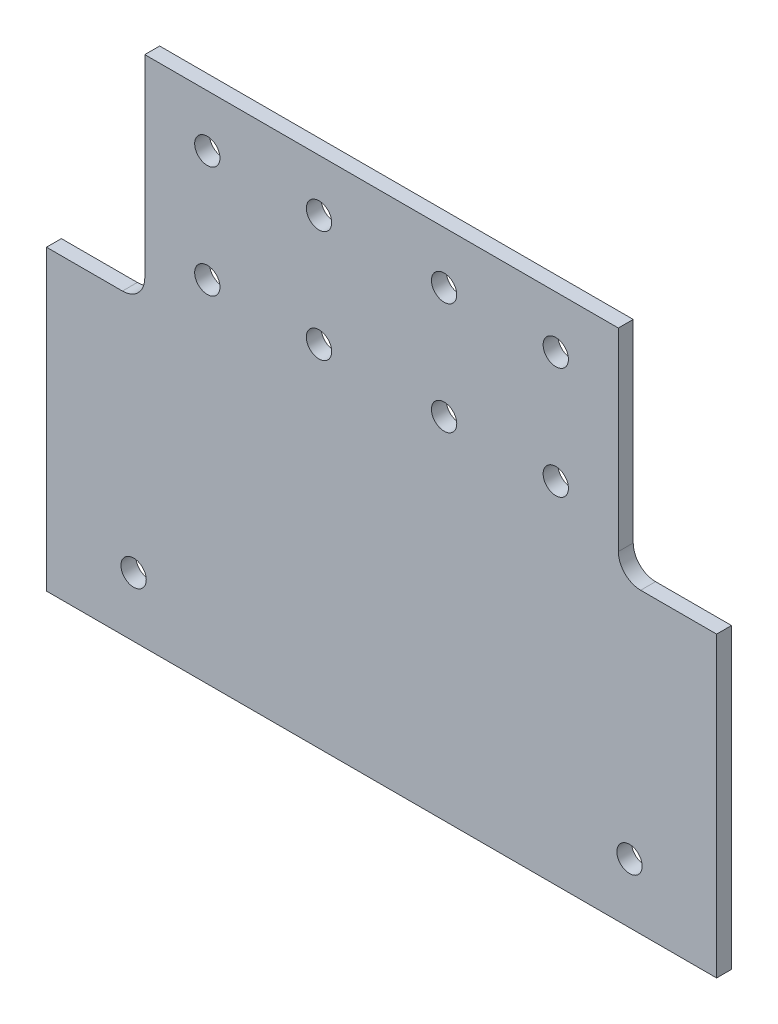
SolidWorks part; units mm, degrees
material "6061 Alloy"
ref_plane "Front Plane" through (0, 0, 0) normal (0, 0, 1) x (1, 0, 0)
ref_plane "Top Plane" through (0, 0, 0) normal (0, 1, 0) x (1, 0, 0)
ref_plane "Right Plane" through (0, 0, 0) normal (1, 0, 0) x (0, 0, -1)
sketch "Sketch1" plane through (0, 0, 0) normal (0, 0, 1) x (1, 0, 0)
  line L0 (0, 230.7484) -> (0, -231.2188) construction
  line L1 (31.8, 0) -> (-31.8, 0)
  line L2 (-31.8, 0) -> (-31.8, -29)
  line L3 (-31.8, -29) -> (-45, -29)
  line L4 (-45, -29) -> (-45, -69)
  line L5 (-45, -69) -> (45, -69)
  line L6 (45, -29) -> (45, -69)
  line L7 (31.8, -29) -> (45, -29)
  line L8 (31.8, 0) -> (31.8, -29)
  point P12 (0, -69)
  point P16 (0, 0)
  dimension "D1" = 63.6
  dimension "D2" = 90
  dimension "D3" = 29
  dimension "D4" = 40
extrude "Base Plate" add sketch "Sketch1" along normal blind 2
hole_wizard "M3 Clearance Hole1" positions "Sketch2" profile "Sketch3" hole size "M3" standard "ANSI Metric" end condition through all
sketch "Sketch2" plane through (0, 0, 2) normal (0, 0, 1) x (1, 0, 0)
  line L0 (0, 5.9983) -> (0, -68.2466) construction
  line L2 (-31.8, -14.5) -> (41.4795, -14.5) construction
  line L3 (-31.8, 0) -> (-31.8, -29) construction
  line L5 (-31.8, -29) -> (-45, -29) construction
  point P0 (-23.4, -7)
  point P2 (-8.4, -7)
  point P4 (-8.4, -22)
  point P6 (-23.4, -22)
  point P8 (-33.3, -61)
  point P24 (-38.4, -29)
  point P25 (33.3, -61)
  point P26 (8.4, -22)
  point P27 (23.4, -22)
  point P28 (8.4, -7)
  point P29 (23.4, -7)
  dimension "D1" = 15
  dimension "D2" = 7.5
  dimension "D3" = 7.5
  dimension "D4" = 8.4
  dimension "D5" = 33.3
  dimension "D6" = 32
sketch "Sketch3" plane through (-23.4, -7, 2) normal (1, 0, 0) x (0, -1, 0)
  line L0 (0, 0) -> (0, 2)
  line L1 (0, 2) -> (1.7, 2)
  line L2 (1.7, 2) -> (1.7, 0)
  line L5 (1.7, 0) -> (0, 0)
  line L11 (0, -6.35) -> (0, 107.95) construction
  dimension "Thru Hole Dia." = 3.4
  dimension "Thru Hole Depth" = 2
fillet "Fillet1" radius 3 2 edges at (31.8, -29, 1) (-31.8, -29, 1)
